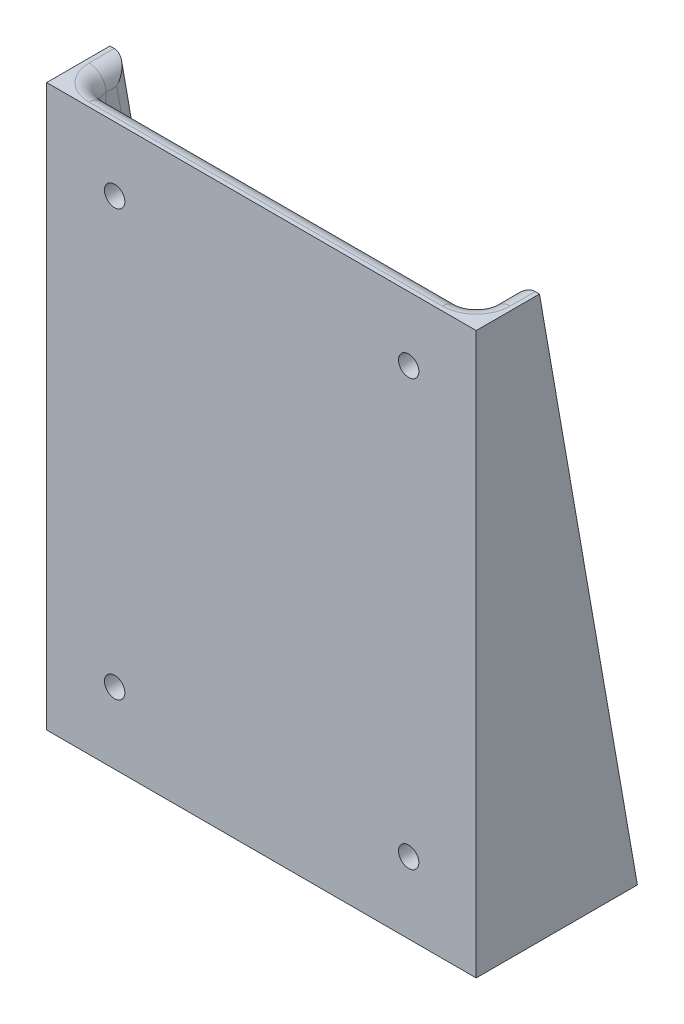
SolidWorks part; units mm, degrees
ref_plane "Front Plane" through (0, 0, 0) normal (0, 0, 1) x (1, 0, 0)
ref_plane "Top Plane" through (0, 0, 0) normal (0, 1, 0) x (1, 0, 0)
ref_plane "Right Plane" through (0, 0, 0) normal (1, 0, 0) x (0, 0, -1)
sketch "Sketch1" plane through (0, 0, 0) normal (1, 0, 0) x (0, 0, -1)
  line L0 (0, 0) -> (24.13, 0)
  line L2 (0, 83.947) -> (0, 0)
  line L3 (24.13, 0) -> (9.4742, 83.947)
  line L4 (9.4742, 83.947) -> (0, 83.947)
  dimension "D1" = 9.4742
  dimension "D2" = 83.947
  dimension "D3" = 24.13
extrude "Boss-Extrude1" add sketch "Sketch1" along normal mid plane 64.3128 contours L2 L0 L3 L4
sketch "Sketch2" plane through (0, 83.947, 0) normal (0, 1, 0) x (1, 0, 0)
  line L0 (-32.1564, 9.4742) -> (-32.1564, 0) construction
  line L1 (-28.9814, 3.175) -> (28.9814, 3.175)
  line L2 (-28.9814, 3.175) -> (-28.9814, 24.13)
  line L3 (-28.9814, 24.13) -> (28.9814, 24.13)
  line L4 (28.9814, 3.175) -> (28.9814, 24.13)
  line L5 (32.1564, 9.4742) -> (32.1564, 0) construction
  line L6 (32.1564, 0) -> (-32.1564, 0) construction
  line L7 (32.1564, 24.13) -> (-32.1564, 24.13) construction
  dimension "D1" = 3.175
  dimension "D2" = 3.175
  dimension "D3" = 3.175
extrude "Cut-Extrude1" cut sketch "Sketch2" against normal offset from surface (80.772 mm away) 3.175 up to face at (0, 0, -12.065)
hole_wizard "#31 (0.12) Diameter Hole1" positions "Sketch3" profile "Sketch4" hole size "#31" standard "ANSI Inch" end condition through all
sketch "Sketch3" plane through (0, 0, 0) normal (0, 0, 1) x (1, 0, 0)
  point P0 (-21.971, 74.3331)
  point P3 (22.0472, 74.3331)
  point P6 (22.0472, 10.668)
  point P9 (-21.971, 10.668)
sketch "Sketch4" plane through (-21.971, 74.3331, 0) normal (1, 0, 0) x (0, -1, 0)
  line L0 (0, 0) -> (0, 24.13)
  line L1 (0, 24.13) -> (1.524, 24.13)
  line L2 (1.524, 24.13) -> (1.524, 0)
  line L5 (1.524, 0) -> (0, 0)
  line L11 (0, -6.35) -> (0, 107.95) construction
  dimension "Thru Hole Dia." = 3.048
  dimension "Thru Hole Depth" = 24.13
hole_wizard "#2 (0.221) Diameter Hole1" positions "Sketch5" profile "Sketch6" hole size "#2" standard "ANSI Inch" end condition through all
sketch "Sketch5" plane through (0, 0, 0) normal (0, -1, 0) x (-1, 0, 0)
  line L0 (-32.1564, 12.065) -> (32.1564, 12.065)
  line L1 (-32.1564, 0) -> (-32.1564, 24.13) construction
  line L2 (32.1564, 0) -> (32.1564, 24.13) construction
  point P0 (-16.9164, 12.065)
  point P2 (16.9164, 12.065)
  point P12 (0, 0)
  point P13 (0, 0)
  dimension "D1" = 15.24
  dimension "D2" = 15.24
sketch "Sketch6" plane through (16.9164, 0, -12.065) normal (1, 0, 0) x (0, 0, -1)
  line L0 (0, 0) -> (0, 83.947)
  line L1 (0, 83.947) -> (2.8067, 83.947)
  line L2 (2.8067, 83.947) -> (2.8067, 0)
  line L5 (2.8067, 0) -> (0, 0)
  line L11 (0, -6.35) -> (0, 107.95) construction
  dimension "Thru Hole Dia." = 5.6134
  dimension "Thru Hole Depth" = 83.947
fillet "Fillet1" radius 2.54 11 edges at (28.9814, 43.561, -16.5249) (28.9814, 83.947, -6.3246) (0, 3.175, -23.5757) (0, 83.947, -3.175) (-28.9814, 43.561, -16.5249) (-28.9814, 3.175, -13.3753) (-28.9814, 83.947, -6.3246) (0, 3.175, -3.175) (28.9814, 3.175, -13.3753) (-28.9814, 43.561, -3.175) (28.9814, 43.561, -3.175)
